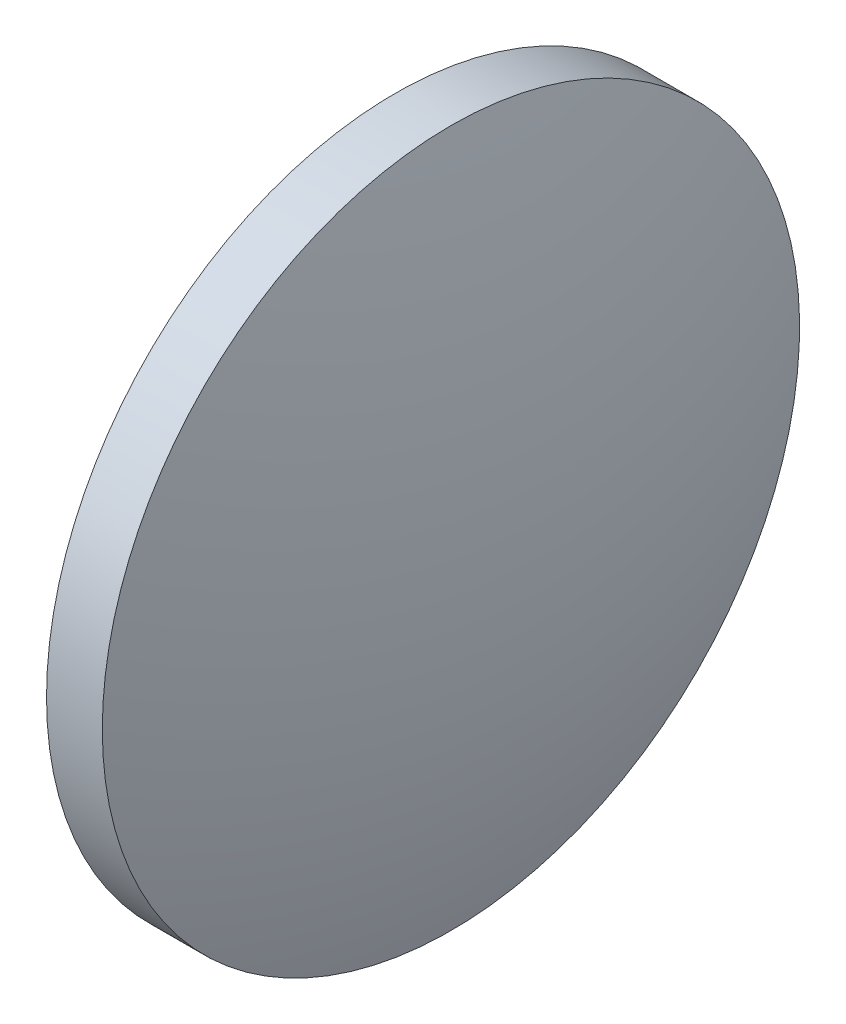
SolidWorks part; units mm, degrees
ref_plane "前视基准面" through (0, 0, 0) normal (0, 0, 1) x (1, 0, 0)
ref_plane "上视基准面" through (0, 0, 0) normal (0, 1, 0) x (1, 0, 0)
ref_plane "右视基准面" through (0, 0, 0) normal (1, 0, 0) x (0, 0, -1)
sketch "草图1" plane through (0, 0, 0) normal (0, 0, 1) x (1, 0, 0)
  line L0 (689.8835, 125.5543) -> (697.912, 125.5543) construction
  line L1 (691.9126, 125.5543) -> (691.9126, 138.0543)
  line L2 (695.8526, 125.5543) -> (691.9126, 125.5543)
  line L5 (691.9126, 138.0543) -> (693.9126, 138.0543)
  arc A0 (695.8526, 125.5543) -> (693.9126, 138.0543) centre (654.612, 125.5543) ccw
revolve "旋转1" add sketch "草图1" angle 360 about L0
